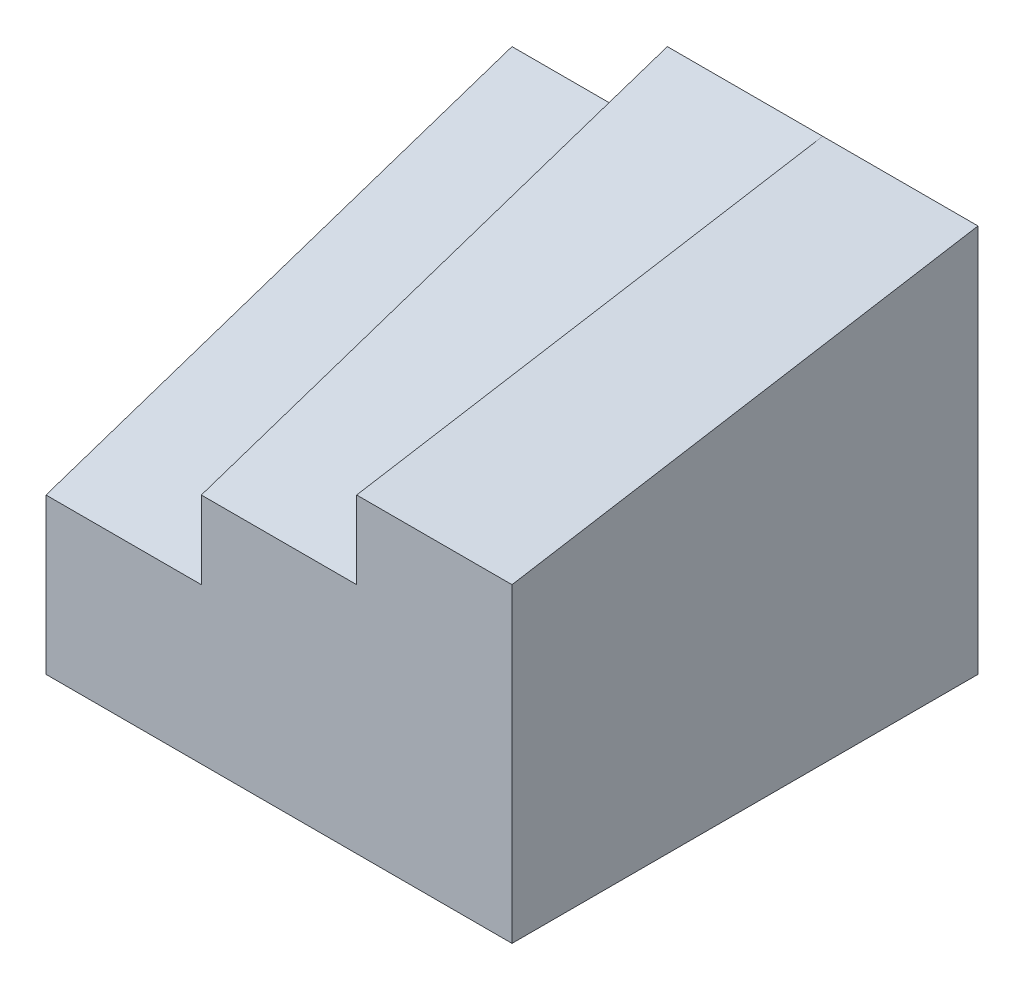
SolidWorks part; units mm, degrees
ref_plane "Front" through (0, 0, 0) normal (0, 0, 1) x (1, 0, 0)
ref_plane "Top" through (0, 0, 0) normal (0, 1, 0) x (1, 0, 0)
ref_plane "Right" through (0, 0, 0) normal (1, 0, 0) x (0, 0, -1)
sketch "Sketch1" plane through (0, 0, 0) normal (0, 1, 0) x (1, 0, 0)
  line L1 (-3, -3) -> (3, -3)
  line L2 (-3, -3) -> (-3, 3)
  line L3 (-3, 3) -> (3, 3)
  line L4 (3, -3) -> (3, 3)
  line L5 (-3, -3) -> (3, 3) construction
  line L6 (-3, 3) -> (3, -3) construction
  point P0 (0, 0)
  dimension "D1" = 6
  dimension "D2" = 6
extrude "Boss-Extrude1" add sketch "Sketch1" along normal blind 5
sketch "Sketch2" plane through (0, 0, 0) normal (1, 0, 0) x (0, 0, -1)
  line L3 (-3, 0) -> (3, 0)
  line L7 (3, 5) -> (-3, 5)
  line L8 (-3, 3) -> (-3, 5)
  line L9 (3, 5) -> (-3, 3)
  line L10 (-3, 0) -> (3, 1)
  line L11 (3, 1) -> (3, 0)
  dimension "D1" = 2
  dimension "D3" = 1
extrude "Cut-Extrude1" cut sketch "Sketch2" against normal mid plane 2
sketch "Sketch3" plane through (-3, 0, 0) normal (-1, 0, 0) x (0, 0, 1)
  line L0 (3, 2) -> (-3, 4)
  line L6 (-3, 0) -> (3, 0)
  line L7 (3, 0) -> (3, 5)
  line L8 (3, 5) -> (-3, 5)
  line L9 (-3, 5) -> (-3, 0)
  line L10 (-3, 0) -> (3, 0)
  line L11 (3, 0) -> (3, 5)
  line L12 (3, 5) -> (-3, 5)
  line L13 (-3, 5) -> (-3, 0)
  line M6 (3, 0) -> (3, 5)
  line M7 (3, 5) -> (-3, 5)
  line M8 (-3, 5) -> (-3, 0)
  dimension "D2" = 3
  dimension "D3" = 1
  dimension "D1" = 0
extrude "Cut-Extrude2" cut sketch "Sketch3" against normal blind 2 contours L0 M6 M7 M8
sketch "Sketch4" plane through (1, 0, 0) normal (-1, 0, 0) x (0, 0, 1)
  line L0 (-3, 5) -> (3, 4)
  line L3 (3, 3) -> (3, 5)
  line L4 (3, 5) -> (-3, 5)
  line L5 (-3, 5) -> (3, 3)
  line L6 (3, 3) -> (3, 5)
  line L7 (3, 5) -> (-3, 5)
  line L8 (-3, 5) -> (3, 3)
  line M4 (3, 3) -> (3, 5)
  line M5 (3, 5) -> (-3, 5)
  dimension "D1" = 0
extrude "Cut-Extrude3" cut sketch "Sketch4" against normal blind 2 contours L0 M5 M4
